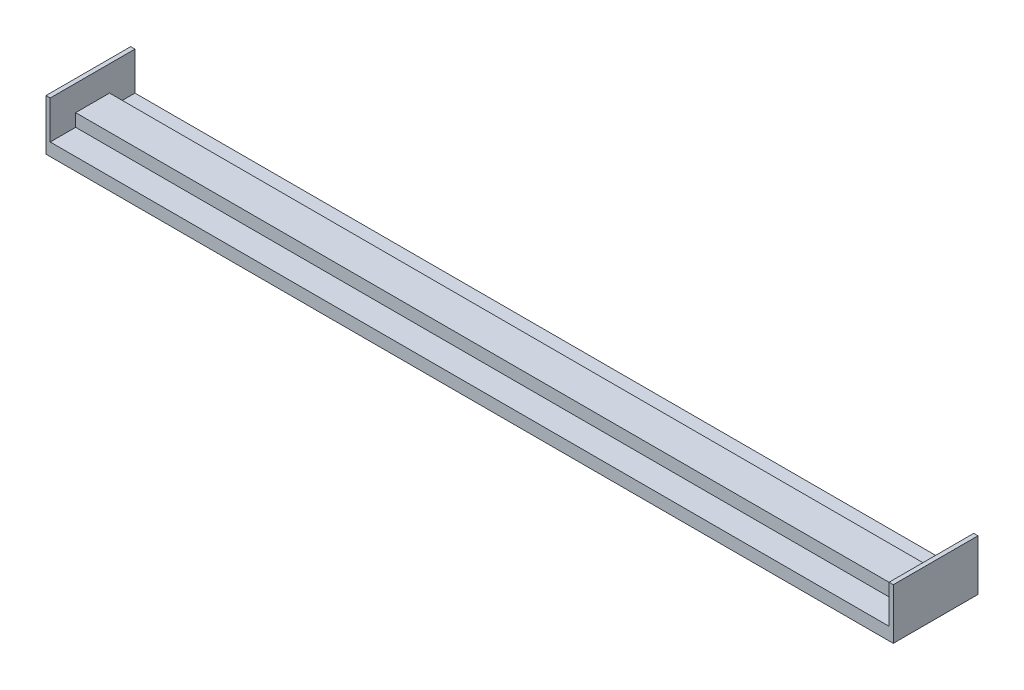
SolidWorks part; units mm, degrees
ref_plane "Front Plane" through (0, 0, 0) normal (0, 0, 1) x (1, 0, 0)
ref_plane "Top Plane" through (0, 0, 0) normal (0, 1, 0) x (1, 0, 0)
ref_plane "Right Plane" through (0, 0, 0) normal (1, 0, 0) x (0, 0, -1)
sketch "Sketch1" plane through (0, 0, 0) normal (1, 0, 0) x (0, 0, -1)
  line L0 (0, 35.2301) -> (0, -50.2831) construction
  line L1 (20, -7.5) -> (-20, -7.5)
  line L2 (20, -7.5) -> (20, 7.5)
  line L3 (20, 7.5) -> (-20, 7.5)
  line L4 (-20, -7.5) -> (-20, 7.5)
  line L5 (20, -7.5) -> (-20, 7.5) construction
  line L6 (20, 7.5) -> (-20, -7.5) construction
  line L7 (-50, -7.5) -> (50, -7.5)
  line L8 (-50, -7.5) -> (-50, -22.5)
  line L9 (-50, -22.5) -> (50, -22.5)
  line L10 (50, -7.5) -> (50, -22.5)
  point P0 (0, 0)
  dimension "D1" = 40
  dimension "D2" = 15
  dimension "D3" = 15
  dimension "D4" = 100
extrude "Boss-Extrude1" add sketch "Sketch1" against normal blind 1000 contours L10 L7 L1 L8 L9 | L4 L1 L2 L3
sketch "Sketch2" plane through (0, 0, 50) normal (0, 0, 1) x (1, 0, 0)
  line L1 (0, -22.5) -> (-5, -22.5)
  line L2 (0, -22.5) -> (0, 37.5)
  line L3 (0, 37.5) -> (-5, 37.5)
  line L4 (-5, -22.5) -> (-5, 37.5)
  dimension "D1" = 60
  dimension "D2" = 5
extrude "Boss-Extrude2" add sketch "Sketch2" against normal blind 100
ref_plane "Plane1" through (-500, 0, 0) normal (-1, 0, 0) x (0, 0, 1)
mirror "Mirror1" about plane through (-500, 0, 0) normal (-1, 0, 0) of "Boss-Extrude2"
